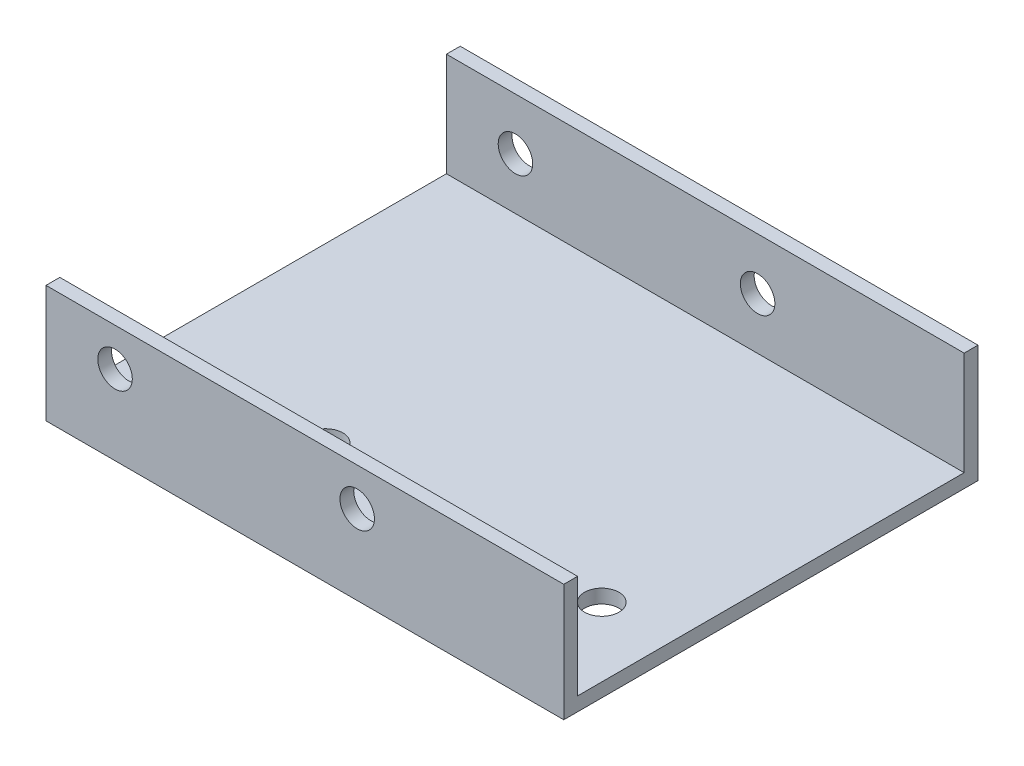
SolidWorks part; units mm, degrees
material "Liga 1060"
ref_plane "Plano frontal" through (0, 0, 0) normal (0, 0, 1) x (1, 0, 0)
ref_plane "Plano superior" through (0, 0, 0) normal (0, 1, 0) x (1, 0, 0)
ref_plane "Plano direito" through (0, 0, 0) normal (1, 0, 0) x (0, 0, -1)
sketch "Esboço1" plane through (0, 0, 0) normal (0, 1, 0) x (1, 0, 0)
  line L1 (37.5, -28) -> (-37.5, -28)
  line L2 (37.5, -28) -> (37.5, 28)
  line L3 (37.5, 28) -> (-37.5, 28)
  line L4 (-37.5, -28) -> (-37.5, 28)
  line L5 (37.5, -28) -> (-37.5, 28) construction
  line L6 (37.5, 28) -> (-37.5, -28) construction
  point P0 (0, 0)
  dimension "D1" = 75
  dimension "D2" = 56
extrude "Ressalto-extrusão1" add sketch "Esboço1" along normal blind 2
sketch "Esboço3" plane through (0, 0, 28) normal (0, 0, 1) x (1, 0, 0)
  line L0 (37.5, 2) -> (37.5, 0) construction
  line L1 (-37.5, 0) -> (37.5, 0)
  line L2 (-37.5, 0) -> (-37.5, 17)
  line L3 (-37.5, 17) -> (37.5, 17)
  line L4 (37.5, 0) -> (37.5, 17)
  dimension "D1" = 17
extrude "Ressalto-extrusão3" add sketch "Esboço3" along normal blind 2
mirror "Espelhar2" about plane through (0, 0, 0) normal (0, 0, 1) of "Ressalto-extrusão3"
sketch "Esboço4" plane through (0, 0, 28) normal (0, 0, -1) x (-1, 0, 0)
  line L0 (37.5, 0) -> (-37.5, 0) construction
  line L1 (-37.5, 0) -> (-37.5, 17) construction
  circle A1 centre (-7.575, 11.5) radius 2.5
  dimension "D2" = 5
  dimension "D3" = 29.925
  dimension "D1" = 11.5
extrude "Corte-extrusão1" cut sketch "Esboço4" against normal up to next
sketch "Esboço5" plane through (0, 0, 30) normal (0, 0, 1) x (1, 0, 0)
  line L0 (-37.5, 0) -> (37.5, 0) construction
  line L1 (-37.5, 17) -> (-37.5, 0) construction
  circle A0 centre (-27.5, 11.5) radius 2.5
  dimension "D1" = 5
  dimension "D2" = 11.5
  dimension "D3" = 10
extrude "Corte-extrusão2" cut sketch "Esboço5" against normal up to next
sketch "Esboço6" plane through (0, 2, 0) normal (0, 1, 0) x (1, 0, 0)
  line L0 (-37.5, 28) -> (-37.5, -28) construction
  line L1 (-37.5, -28) -> (37.5, -28) construction
  circle A1 centre (27.5, -14.5) radius 2.5 construction
  circle A2 centre (-12.5, -14.5) radius 2.5
  circle A3 centre (27.5, -14.5) radius 2.5
  dimension "D1" = 25
  dimension "D2" = 13.5
  dimension "D3" = 5
extrude "Corte-extrusão3" cut sketch "Esboço6" against normal blind 2
sketch "Sketch1" plane through (0, 0, -30) normal (0, 0, -1) x (-1, 0, 0)
  line L0 (37.5, 0) -> (-37.5, 0) construction
  line L2 (-37.5, 0) -> (-37.5, 17) construction
  circle A0 centre (-7.575, 9.5) radius 2.5
  dimension "D1" = 5
  dimension "D3" = 29.925
  dimension "D2" = 9.5
extrude "Cut-Extrude1" cut sketch "Sketch1" against normal up to next
sketch "Sketch2" plane through (0, 0, -30) normal (0, 0, -1) x (-1, 0, 0)
  line L0 (37.5, 17) -> (37.5, 0) construction
  line L1 (37.5, 0) -> (-37.5, 0) construction
  circle A0 centre (27.5, 9.5) radius 2.5
  dimension "D1" = 5
  dimension "D3" = 9.5
  dimension "D2" = 10
extrude "Cut-Extrude2" cut sketch "Sketch2" against normal up to next
